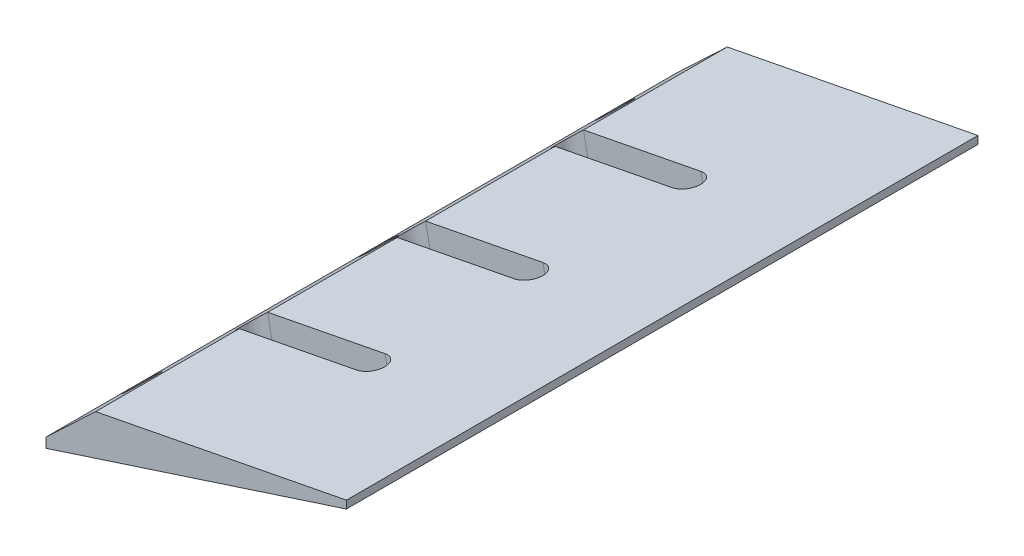
SolidWorks part; units mm, degrees
ref_plane "Front Plane" through (0, 0, 0) normal (0, 0, 1) x (1, 0, 0)
ref_plane "Top Plane" through (0, 0, 0) normal (0, 1, 0) x (1, 0, 0)
ref_plane "Right Plane" through (0, 0, 0) normal (1, 0, 0) x (0, 0, -1)
sketch "Sketch1" plane through (0, 0, 0) normal (0, 0, 1) x (1, 0, 0)
  line L0 (0, 0) -> (-78.5302, -15.2647)
  line L1 (-1000, 0) -> (49000, 0) construction
  line L2 (0, 0) -> (-95.1057, -30.9017)
  line L3 (-95.1057, -30.9017) -> (-78.5302, -15.2647)
  dimension "D1" = 18
  dimension "D2" = 11
  dimension "D3" = 100
  dimension "D4" = 80
extrude "Boss-Extrude1" add sketch "Sketch1" along normal blind 160
ref_plane "Plane1" through (-3.0902, 9.5106, 0) normal (-0.309, 0.9511, 0) x (0.9511, 0.309, 0)
sketch "Sketch3" plane through (-3.0902, 9.5106, 0) normal (-0.309, 0.9511, 0) x (0.9511, 0.309, 0)
  line L0 (-79.4037, 0) -> (-100, 0) construction
  line L1 (-1079.4037, -80) -> (48920.5963, -80) construction
  line L2 (-79.4037, -160) -> (-79.4037, 0) construction
  circle A0 centre (-89.7018, -20) radius 1.5
  circle A1 centre (-89.7018, -80) radius 1.5
  circle A2 centre (-89.7018, -140) radius 1.5
  point P0 (-89.7018, -20)
  point P4 (-89.7018, -140)
  point P8 (-79.4037, -80)
  point P9 (-89.7018, -80)
  dimension "D2" = 3
  dimension "D1" = 20
extrude "Cut-Extrude1" cut sketch "Sketch3" against normal through all
sketch "Sketch4" plane through (-3.0902, 9.5106, 0) normal (-0.309, 0.9511, 0) x (0.9511, 0.309, 0)
  circle A0 centre (-89.7018, -20) radius 4
  circle A1 centre (-89.7018, -80) radius 4
  circle A2 centre (-89.7018, -140) radius 4
extrude "Cut-Extrude2" cut sketch "Sketch4" against normal blind 8
sketch "Sketch5" plane through (-0.6004, -0.1167, 0) normal (-0.1908, 0.9816, 0) x (0.9816, 0.1908, 0)
  line L0 (-89.7018, -80) -> (49910.2982, -80) construction
  line L1 (-79.1446, -40) -> (-50079.1446, -40) construction
  line L2 (-79.1563, -120) -> (-50079.1563, -120) construction
  line L3 (-49.1092, -120) -> (-79.3884, -120) construction
  line L4 (-49.1092, -123.6) -> (-79.3884, -123.6)
  line L5 (-49.1092, -116.4) -> (-79.3884, -116.4)
  line L6 (-49.1092, -80) -> (-79.3884, -80) construction
  line L7 (-49.1092, -83.6) -> (-79.3884, -83.6)
  line L8 (-49.1092, -76.4) -> (-79.3884, -76.4)
  line L9 (-49.1092, -40) -> (-79.3884, -40) construction
  line L10 (-49.1092, -43.6) -> (-79.3884, -43.6)
  line L11 (-49.1092, -36.4) -> (-79.3884, -36.4)
  line L12 (-79.3884, -160) -> (-79.3884, 0) construction
  arc A0 (-49.1092, -123.6) -> (-49.1092, -116.4) centre (-49.1092, -120) ccw
  arc A1 (-79.3884, -116.4) -> (-79.3884, -123.6) centre (-79.3884, -120) ccw
  arc A2 (-49.1092, -83.6) -> (-49.1092, -76.4) centre (-49.1092, -80) ccw
  arc A3 (-79.3884, -76.4) -> (-79.3884, -83.6) centre (-79.3884, -80) ccw
  arc A4 (-49.1092, -43.6) -> (-49.1092, -36.4) centre (-49.1092, -40) ccw
  arc A5 (-79.3884, -36.4) -> (-79.3884, -43.6) centre (-79.3884, -40) ccw
  point P2 (18.7174, -80)
  point P9 (-64.2488, -120)
  point P14 (-64.2488, -80)
  point P21 (-64.2488, -40)
  point P28 (0, 0)
  point P29 (18.7174, -40)
  point P30 (-49.1092, -120)
  point P31 (-49.1092, -80)
  point P32 (-49.1092, -40)
  point P33 (-79.3884, -120)
  point P36 (-79.3884, -80)
  point P37 (-79.3884, -40)
  dimension "D3" = 7.2
  dimension "D4" = 7.2
  dimension "D5" = 7.2
extrude "Cut-Extrude3" cut sketch "Sketch5" against normal through all both and the other way through all
sketch "Sketch6" plane through (0, 0, 160) normal (0, 0, 1) x (1, 0, 0)
  line L0 (-15, 4.4925) -> (-15, -6.9698)
  line L1 (-15, -6.9698) -> (0, -6.9698)
  line L2 (0, -6.9698) -> (0, 6.9698)
  line L3 (0, 6.9698) -> (-15, 4.4925)
  line L4 (-91.1057, -36.385) -> (-91.1057, -21.7848)
  line L5 (-91.1057, -21.7848) -> (-95.1057, -21.7848)
  line L6 (-95.1057, -21.7848) -> (-95.1057, -36.385)
  line L7 (-95.1057, -36.385) -> (-91.1057, -36.385)
  point P6 (0, 2.4774)
  point P11 (0, 0)
  point P12 (-95.1057, -36.385)
  dimension "D1" = 4
  dimension "D2" = 15
extrude "Cut-Extrude4" cut sketch "Sketch6" against normal through all both and the other way through all
